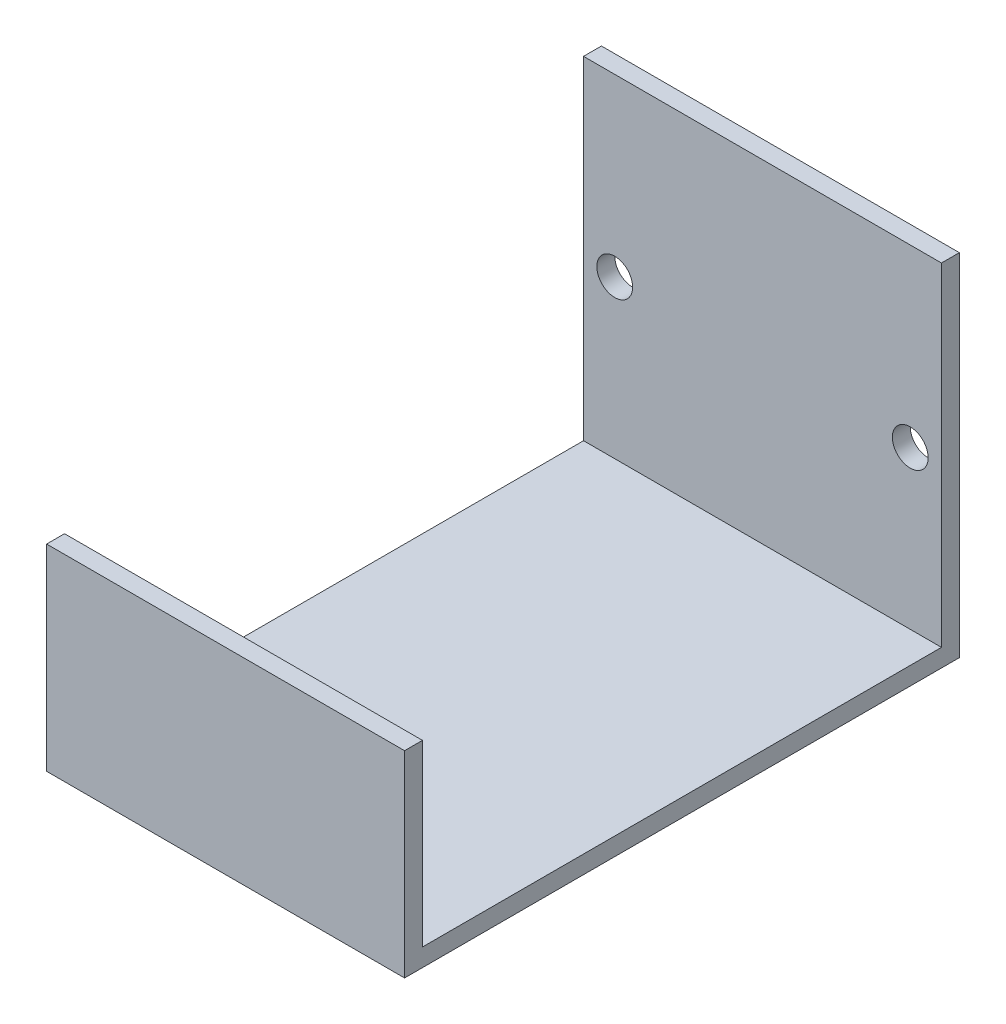
SolidWorks part; units mm, degrees
ref_plane "Front Plane" through (0, 0, 0) normal (0, 0, 1) x (1, 0, 0)
ref_plane "Top Plane" through (0, 0, 0) normal (0, 1, 0) x (1, 0, 0)
ref_plane "Right Plane" through (0, 0, 0) normal (1, 0, 0) x (0, 0, -1)
sketch "Sketch1" plane through (0, 0, 0) normal (0, 0, 1) x (1, 0, 0)
  line L1 (-10, -9.8) -> (10, -9.8)
  line L2 (-10, -9.8) -> (-10, 9.8)
  line L3 (-10, 9.8) -> (10, 9.8)
  line L4 (10, -9.8) -> (10, 9.8)
  line L5 (-10, -9.8) -> (10, 9.8) construction
  line L6 (-10, 9.8) -> (10, -9.8) construction
  circle A0 centre (-8.256, 0) radius 1
  circle A1 centre (8.256, 0) radius 1
  point P0 (0, 0)
  dimension "D3" = 2
  dimension "D4" = 2
  dimension "D5" = 14.512
  dimension "D6" = 7.256
  dimension "D1" = 20
  dimension "D2" = 19.6
extrude "Boss-Extrude1" add sketch "Sketch1" along normal blind 1
sketch "Sketch2" plane through (0, 0, 1) normal (0, 0, 1) x (1, 0, 0)
  line L0 (10, -9.8) -> (10, 9.8) construction
  line L1 (-10, -9.8) -> (10, -9.8)
  line L2 (-10, -9.8) -> (-10, -8.8)
  line L3 (-10, -8.8) -> (10, -8.8)
  line L4 (10, -9.8) -> (10, -8.8)
  dimension "D1" = 1
extrude "Boss-Extrude2" add sketch "Sketch2" along normal blind 30
sketch "Sketch3" plane through (0, -8.8, 0) normal (0, 1, 0) x (1, 0, 0)
  line L0 (-10, -31) -> (-10, -1) construction
  line L1 (10, -31) -> (-10, -31)
  line L2 (10, -31) -> (10, -30)
  line L3 (10, -30) -> (-10, -30)
  line L4 (-10, -31) -> (-10, -30)
  dimension "D1" = 1
extrude "Boss-Extrude3" add sketch "Sketch3" along normal blind 10
